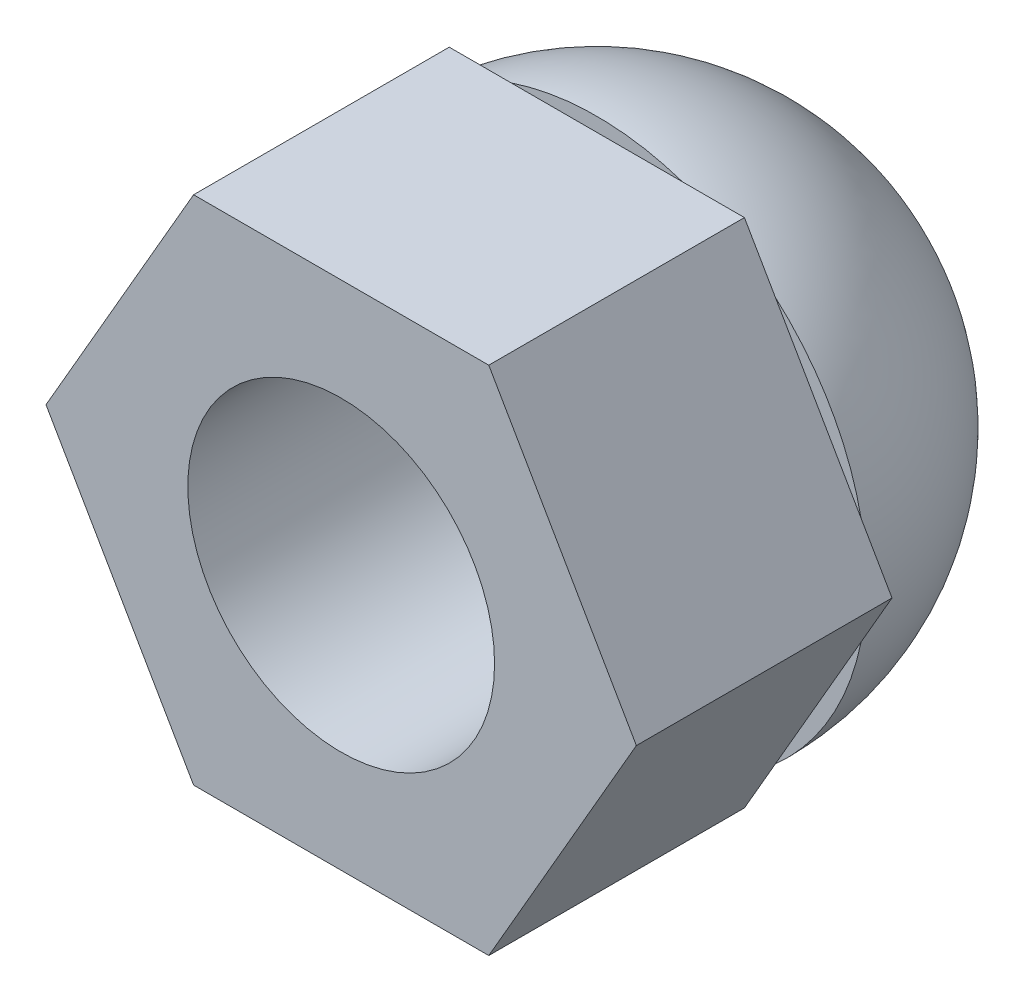
SolidWorks part; units mm, degrees
ref_plane "Plano frontal" through (0, 0, 0) normal (0, 0, 1) x (1, 0, 0)
ref_plane "Plano superior" through (0, 0, 0) normal (0, 1, 0) x (1, 0, 0)
ref_plane "Plano direito" through (0, 0, 0) normal (1, 0, 0) x (0, 0, -1)
sketch "Esboço1" plane through (0, 0, 0) normal (0, 0, 1) x (1, 0, 0)
  line L1 (2.8868, 5) -> (-2.8868, 5)
  line L2 (-2.8868, 5) -> (-5.7735, 0)
  line L3 (-5.7735, 0) -> (-2.8868, -5)
  line L4 (-2.8868, -5) -> (2.8868, -5)
  line L5 (2.8868, -5) -> (5.7735, 0)
  line L6 (5.7735, 0) -> (2.8868, 5)
  circle A0 centre (0, 0) radius 5 construction
  circle A1 centre (0, 0) radius 3
  dimension "D1" = 6
  dimension "D2" = 10
extrude "Ressalto-extrusão1" add sketch "Esboço1" along normal blind 5
sketch "Esboço2" plane through (0, 0, 0) normal (0, 1, 0) x (1, 0, 0)
  line L0 (0, 0) -> (5.2735, 0)
  line L1 (0, 5.2735) -> (0, 0)
  arc A0 (5.2735, 0) -> (0, 5.2735) centre (0, 0) ccw
  dimension "D1" = 0.5
revolve "Revolução1" add sketch "Esboço2" angle 360 about L1
